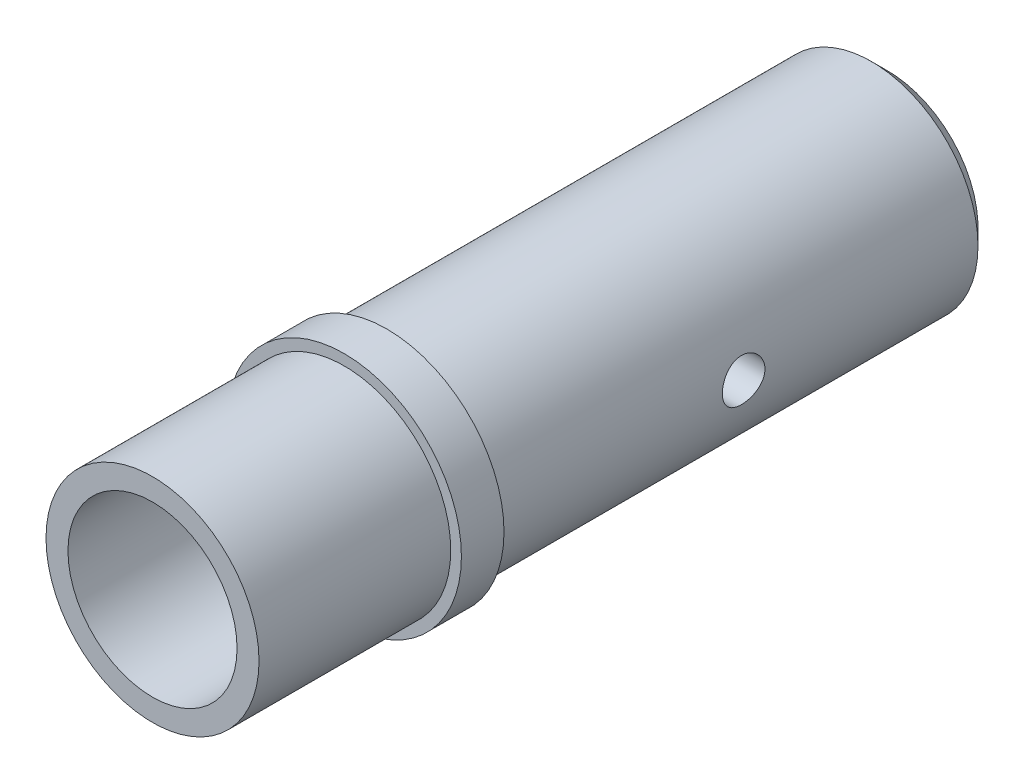
SolidWorks part; units mm, degrees
ref_plane "Płaszczyzna XY" through (0, 0, 0) normal (0, 0, 1) x (1, 0, 0)
ref_plane "Płaszczyzna XZ" through (0, 0, 0) normal (0, 1, 0) x (1, 0, 0)
ref_plane "Płaszczyzna YZ" through (0, 0, 0) normal (1, 0, 0) x (0, 0, -1)
sketch "Szkic1" plane through (0, 0, 0) normal (0, 0, 1) x (1, 0, 0)
  circle A0 centre (0, 0) radius 7.9375
  circle A1 centre (0, 0) radius 10
  dimension "D1" = 15.875
  dimension "D2" = 20
extrude "Dodanie-wyciągnięcie1" add sketch "Szkic1" along normal blind 18
ref_plane "Płaszczyzna1" through (0, 0, 0) normal (0, 0, -1) x (-1, 0, 0)
sketch "Szkic2" plane through (0, 0, 0) normal (0, 0, -1) x (-1, 0, 0)
  circle A0 centre (0, 0) radius 11
  circle A1 centre (0, 0) radius 7.9375
  dimension "D1" = 22
extrude "Dodanie-wyciągnięcie2" add sketch "Szkic2" along normal blind 4
sketch "Szkic3" plane through (0, 0, -4) normal (0, 0, -1) x (-1, 0, 0)
  circle A0 centre (0, 0) radius 10
  circle A1 centre (0, 0) radius 6
  dimension "D1" = 12
  dimension "D2" = 20
extrude "Dodanie-wyciągnięcie3" add sketch "Szkic3" along normal blind 47
chamfer "Sfazowanie1" distance 1.5 angle 45 1 edges at (-10, 0, -51)
sketch "Szkic6" plane through (0, 0, 0) normal (1, 0, 0) x (0, 0, -1)
  line L0 (4, 0) -> (51, 0) construction
  line L1 (4, -10) -> (4, 10) construction
  line L2 (51, -8.5) -> (51, 8.5) construction
  circle A0 centre (27.5, 0) radius 2
extrude "Wytnij-wyciągnięcie1" cut sketch "Szkic6" against normal mid plane 30 contours A0
